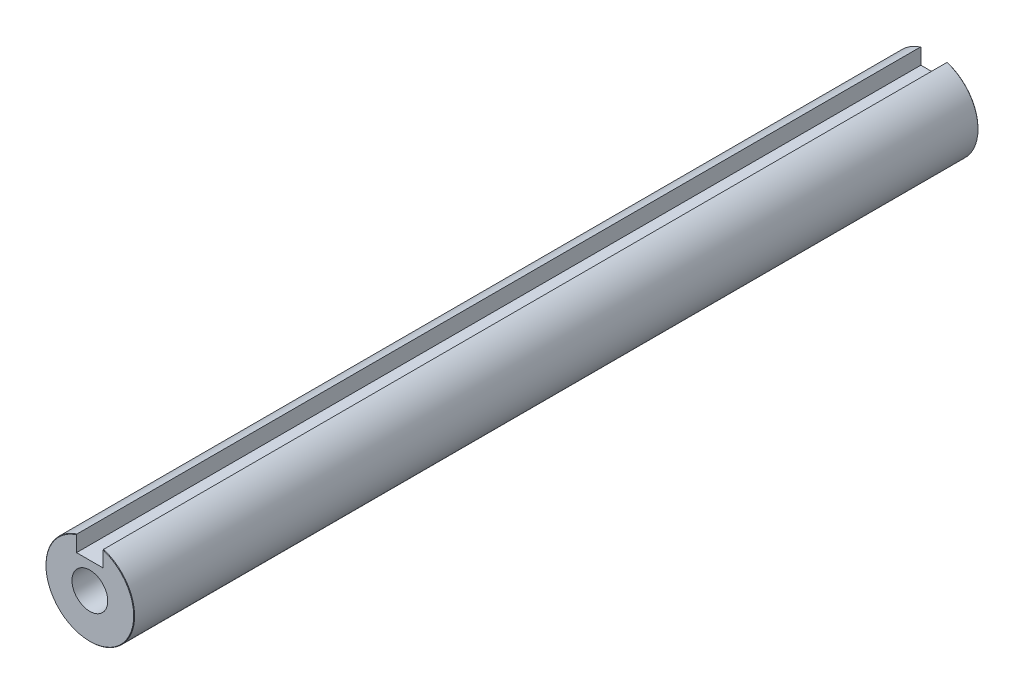
SolidWorks part; units mm, degrees
ref_plane "Front Plane" through (0, 0, 0) normal (0, 0, 1) x (1, 0, 0)
ref_plane "Top Plane" through (0, 0, 0) normal (0, 1, 0) x (1, 0, 0)
ref_plane "Right Plane" through (0, 0, 0) normal (1, 0, 0) x (0, 0, -1)
sketch "Sketch1" plane through (0, 0, 0) normal (1, 0, 0) x (0, 0, -1)
  line L0 (0, 0) -> (0, 5) construction
  line L1 (-47.625, 5) -> (47.625, 5)
  line L2 (-47.625, 5) -> (-47.625, -5)
  line L3 (-47.625, -5) -> (47.625, -5)
  line L4 (47.625, 5) -> (47.625, -5)
  line L5 (-47.625, 5) -> (47.625, -5) construction
  line L6 (-47.625, -5) -> (47.625, 5) construction
  line L7 (0, 0) -> (0, -5) construction
  point P0 (0, 0)
  point P8 (-36.125, 5)
  point P10 (36.125, 5)
  point P11 (-32.2917, -5)
  point P12 (34.346, -5)
  dimension "Diameter" = 10
  dimension "Length" = 95.25
  dimension "D1" = 11.5
  dimension "D2" = 11.5
  dimension "Keyway Length" = 95.25
  dimension "D3" = 13.279
  dimension "D5" = 15.3333
sketch "Sketch2" plane through (0, 0, 0) normal (0, 0, 1) x (1, 0, 0)
  line L0 (0, 0) -> (0, 5) construction
  line L2 (1.5, 2.9697) -> (-1.5, 2.9697)
  line L3 (1.5, 2.9697) -> (1.5, 4.7697)
  line L4 (1.5, 4.7697) -> (-1.5, 4.7697)
  line L5 (-1.5, 2.9697) -> (-1.5, 4.7697)
  line L6 (1.5, 2.9697) -> (-1.5, 4.7697) construction
  line L7 (1.5, 4.7697) -> (-1.5, 2.9697) construction
  circle A0 centre (0, 0) radius 5
  point P3 (0, 3.8697)
  dimension "Keyway Width" = 3
  dimension "Keyway Depth" = 1.8
sketch "Sketch3" plane through (0, 0, 0) normal (0, 0, 1) x (1, 0, 0)
  line L1 (-1.5, 2.9697) -> (-1.5, 4.7697) construction
  line L2 (1.5, 2.9697) -> (-1.5, 2.9697) construction
  line L3 (1.5, 2.9697) -> (1.5, 4.7697) construction
  line L5 (-1.5, 2.9697) -> (-1.5, 4.7697)
  line L6 (1.5, 2.9697) -> (-1.5, 2.9697)
  line L7 (1.5, 2.9697) -> (1.5, 4.7697)
  circle A0 centre (0, 0) radius 5 construction
  arc A1 (-1.5, 4.7697) -> (1.5, 4.7697) centre (0, 0) ccw
extrude "Boss-Extrude1" add sketch "Sketch3" along normal up to vertex (47.625 mm away) and the other way up to vertex (47.625 mm away) up to point (0, 5, 47.625) other way up to point (0, 5, -47.625)
chamfer "Chamfer1" distance 0.05 angle 45 2 edges at (0, -5, 47.625) (0, -5, -47.625)
hole_wizard "Tap Drill for #10-32 Tap2" positions "3DSketch1" profile "Sketch4" hole size "#10-32" standard "ANSI Inch"
sketch3d "3DSketch1"
  arc A0 (1.5, 4.7173, -47.625) -> (-1.5, 4.7173, -47.625) centre (0, 0, -47.625) ccw construction
  point P0 (0, 0, -47.625)
  point P6 (0, 0, -52.575)
sketch "Sketch4" plane through (0, 0, -47.625) normal (1, 0, 0) x (0, 1, 0)
  line L0 (0, 0) -> (0, 17.0883)
  line L1 (0, 17.0883) -> (2.0193, 15.875)
  line L2 (2.0193, 15.875) -> (2.0193, 0)
  line L5 (2.0193, 0) -> (0, 0)
  line L10 (0, 17.0883) -> (-2.0193, 15.875) construction
  line L11 (0, -6.35) -> (0, 107.95) construction
  dimension "Hole Dia." = 4.0386
  dimension "Hole Depth" = 15.875
  dimension "Drill Angle" = 118
hole_wizard "Tap Drill for #10-32 Tap1" positions "3DSketch2" profile "Sketch5" hole size "#10-32" standard "ANSI Inch"
sketch3d "3DSketch2"
  arc A0 (-1.5, 4.7173, 47.625) -> (1.5, 4.7173, 47.625) centre (0, 0, 47.625) ccw construction
  point P0 (0, 0, 47.625)
  point P6 (0, 0, 52.575)
sketch "Sketch5" plane through (0, 0, 47.625) normal (1, 0, 0) x (0, -1, 0)
  line L0 (0, 0) -> (0, 10.7383)
  line L1 (0, 10.7383) -> (2.0193, 9.525)
  line L2 (2.0193, 9.525) -> (2.0193, 0)
  line L5 (2.0193, 0) -> (0, 0)
  line L10 (0, 10.7383) -> (-2.0193, 9.525) construction
  line L11 (0, -6.35) -> (0, 107.95) construction
  dimension "Hole Dia." = 4.0386
  dimension "Hole Depth" = 9.525
  dimension "Drill Angle" = 118
equation "\"D2@Sketch1\"=1.15*\"Diameter@Sketch1\""
equation "\"D1@Sketch1\"=\"D2@Sketch1\""
equation "\"D1@Chamfer1\"=\"Diameter@Sketch1\"*.005"
equation "\"D3@Sketch1\"=\"D2@Sketch1\"/(2*tan(.5236*180/pi))*4/3"
equation "\"D5@Sketch1\" = 4 / 3 * \"D2@Sketch1\""
